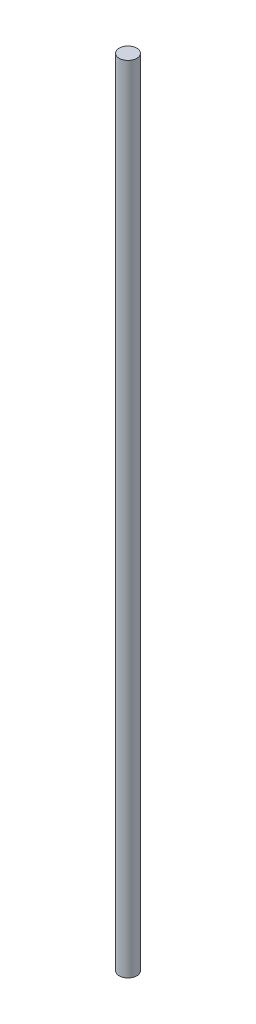
SolidWorks part; units mm, degrees
ref_plane "Front Plane" through (0, 0, 0) normal (0, 0, 1) x (1, 0, 0)
ref_plane "Top Plane" through (0, 0, 0) normal (0, 1, 0) x (1, 0, 0)
ref_plane "Right Plane" through (0, 0, 0) normal (1, 0, 0) x (0, 0, -1)
sketch "Sketch1" plane through (0, 0, 0) normal (0, 1, 0) x (1, 0, 0)
  circle A0 centre (0, 0) radius 4
extrude "Boss-Extrude1" add sketch "Sketch1" along normal blind 360
